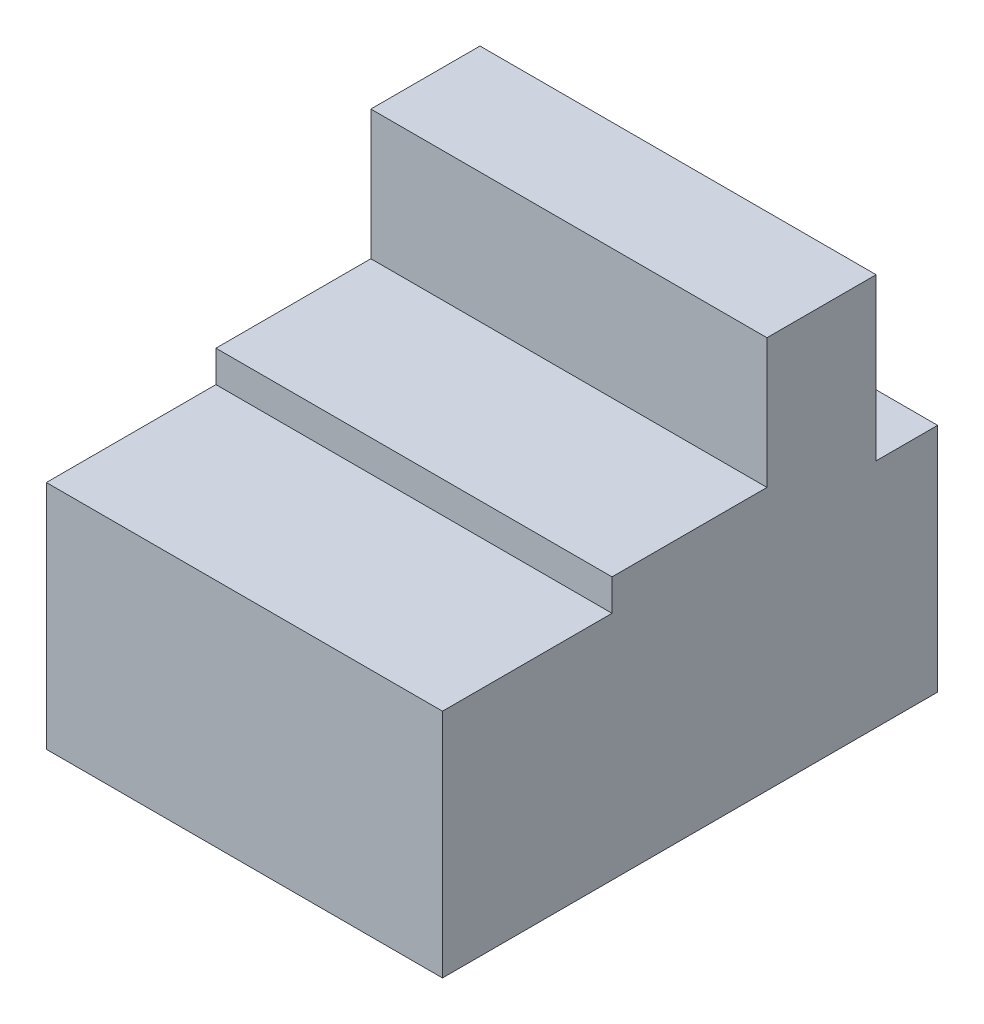
SolidWorks part; units mm, degrees
ref_plane "Front Plane" through (0, 0, 0) normal (0, 0, 1) x (1, 0, 0)
ref_plane "Top Plane" through (0, 0, 0) normal (0, 1, 0) x (1, 0, 0)
ref_plane "Right Plane" through (0, 0, 0) normal (1, 0, 0) x (0, 0, -1)
sketch "Sketch1" plane through (0, 0, 0) normal (0, 1, 0) x (1, 0, 0)
  line L1 (0, 0) -> (152.4, 0)
  line L2 (0, 0) -> (0, 190.5)
  line L3 (0, 190.5) -> (152.4, 190.5)
  line L4 (152.4, 0) -> (152.4, 190.5)
  dimension "D1" = 152.4
  dimension "D2" = 190.5
extrude "Boss-Extrude1" add sketch "Sketch1" along normal blind 88.9 contours L2 L3 L4 L1
sketch "Sketch2" plane through (0, 0, 0) normal (1, 0, 0) x (0, 0, -1)
  line L0 (65.2297, 88.9) -> (166.8297, 88.9)
  line L2 (166.8297, 88.9) -> (166.8297, 150.9217)
  line L3 (166.8297, 150.9217) -> (124.8334, 150.9217)
  line L4 (124.8334, 150.9217) -> (124.8334, 101.0412)
  line L5 (124.8334, 101.0412) -> (65.2297, 101.0412)
  line L6 (65.2297, 101.0412) -> (65.2297, 88.9)
  dimension "D1" = 65.2297
  dimension "D2" = 101.6
  dimension "D3" = 59.6036
  dimension "D4" = 62.0217
  dimension "D5" = 41.9964
  dimension "D6" = 12.1412
extrude "Boss-Extrude2" add sketch "Sketch2" along normal up to surface (152.4 mm away) up to face at (152.4, 44.45, -95.25)
